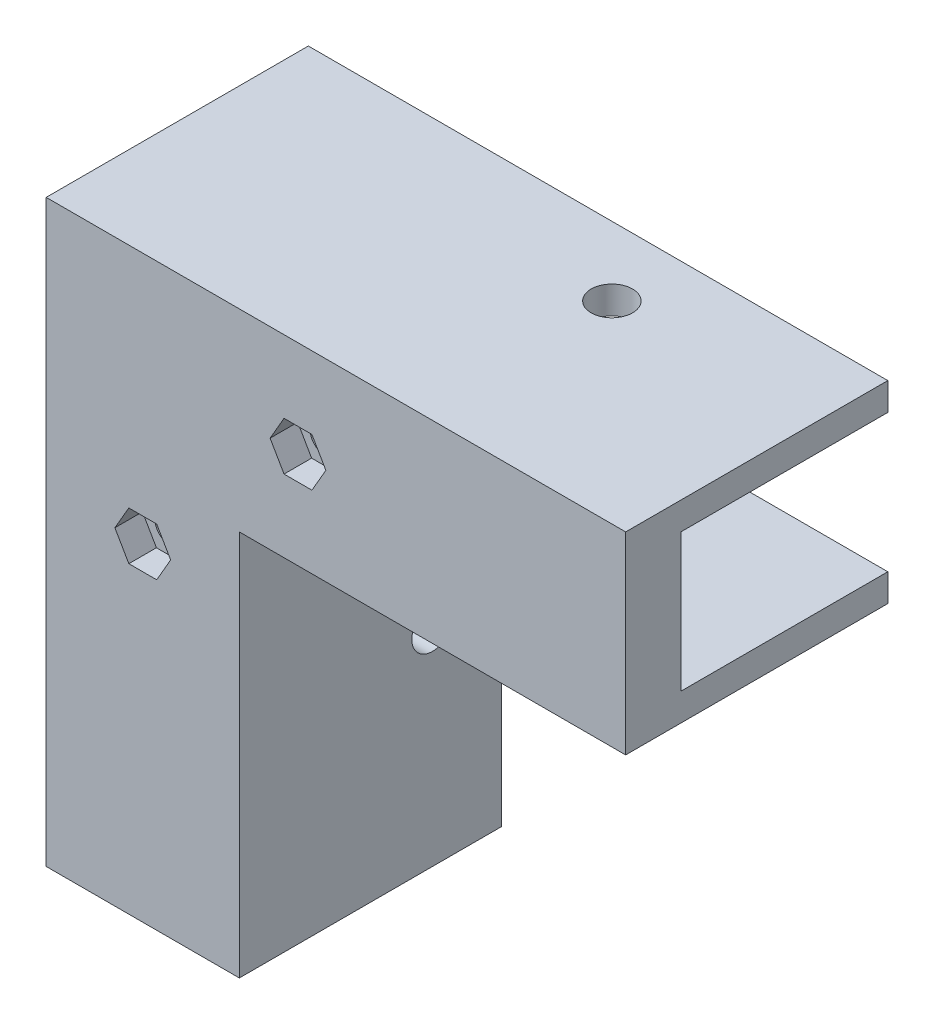
SolidWorks part; units mm, degrees
ref_plane "Plan de face" through (0, 0, 0) normal (0, 0, 1) x (1, 0, 0)
ref_plane "Plan de dessus" through (0, 0, 0) normal (0, 1, 0) x (1, 0, 0)
ref_plane "Plan de droite" through (0, 0, 0) normal (1, 0, 0) x (0, 0, -1)
sketch "Esquisse1" plane through (0, 0, 0) normal (0, 0, 1) x (1, 0, 0)
  line L0 (0, 0) -> (0, 60)
  line L1 (0, 60) -> (60, 60)
  line L2 (60, 60) -> (60, 80)
  line L3 (60, 80) -> (-20, 80)
  line L4 (-20, 80) -> (-20, 0)
  line L5 (-20, 0) -> (0, 0)
  dimension "D1" = 60
  dimension "D2" = 60
  dimension "D3" = 20
  dimension "D4" = 20
extrude "Boss.-Extru.1" add sketch "Esquisse1" along normal blind 8
sketch "Esquisse2" plane through (0, 0, 8) normal (0, 0, 1) x (1, 0, 0)
  line L0 (-12.0207, 51) -> (-7.9793, 44) construction
  line L1 (-20, 80) -> (-20, 0) construction
  line L3 (-5.9585, 47.5) -> (-14.0415, 47.5) construction
  line L5 (60, 80) -> (-20, 80) construction
  line L6 (0, 0) -> (0, 60) construction
  line L7 (-14.0415, 47.5) -> (-12.0207, 51)
  line L8 (-12.0207, 51) -> (-7.9793, 51)
  line L9 (-7.9793, 51) -> (-5.9585, 47.5)
  line L10 (-5.9585, 47.5) -> (-7.9793, 44)
  line L11 (-7.9793, 44) -> (-12.0207, 44)
  line L12 (-12.0207, 44) -> (-14.0415, 47.5)
  line L13 (10.4793, 66.5) -> (14.5207, 73.5) construction
  line L14 (16.5415, 70) -> (8.4585, 70) construction
  line L15 (-5.9585, 47.5) -> (-6.29, 47.0056)
  line L20 (-12.0207, 44) -> (-12.0207, 51) construction
  line L23 (8.4585, 70) -> (10.4793, 73.5)
  line L24 (10.4793, 73.5) -> (14.5207, 73.5)
  line L25 (14.5207, 73.5) -> (16.5415, 70)
  line L26 (16.5415, 70) -> (14.5207, 66.5)
  line L27 (14.5207, 66.5) -> (10.4793, 66.5)
  line L28 (10.4793, 66.5) -> (8.4585, 70)
  line L31 (16.5415, 70) -> (16.21, 69.5056)
  line L36 (10.4793, 66.5) -> (10.4793, 73.5) construction
  point P26 (-10, 47.5)
  point P27 (12.5, 70)
  dimension "D2" = 32.5
  dimension "D3" = 7
  dimension "D4" = 7
  dimension "D6" = 120
  dimension "D7" = 30
  dimension "D8" = 7
  dimension "D9" = 7
  dimension "D10" = 7
  dimension "D11" = 120
  dimension "D12" = 30
  dimension "D13" = 10
  dimension "D14" = 10
  dimension "D15" = 32.5
extrude "Enlèv. mat.-Extru.1" cut sketch "Esquisse2" against normal blind 4
sketch "Esquisse3" plane through (0, 0, 4) normal (0, 0, 1) x (1, 0, 0)
  line L0 (-7.9793, 51) -> (-5.9585, 47.5) construction
  line L1 (-14.0415, 47.5) -> (-12.0207, 51) construction
  line L3 (10.4793, 73.5) -> (14.5207, 73.5) construction
  line L4 (16.5415, 70) -> (14.5207, 66.5) construction
  circle A0 centre (-10, 47.5) radius 2.25
  circle A1 centre (12.5, 70) radius 2.25
  dimension "D1" = 3.5
  dimension "D2" = 3.5
  dimension "D3" = 4.5
  dimension "D4" = 4.5
  dimension "D5" = 3.5
  dimension "D6" = 3.5
extrude "Enlèv. mat.-Extru.2" cut sketch "Esquisse3" against normal through all
sketch "Esquisse4" plane through (0, 0, 8) normal (0, 0, 1) x (1, 0, 0)
  line L0 (0, 0) -> (0, 60)
  line L2 (0, 60) -> (60, 60)
  line L3 (60, 60) -> (60, 56)
  line L4 (60, 56) -> (4, 56)
  line L5 (4, 56) -> (4, 0)
  line L6 (4, 0) -> (0, 0)
  line L7 (60, 80) -> (60, 84)
  line L8 (60, 84) -> (-24, 84)
  line L9 (-24, 84) -> (-24, 0)
  line L10 (-24, 0) -> (-20, 0)
  line L11 (-20, 0) -> (-20, 80)
  line L12 (-20, 80) -> (60, 80)
  dimension "D1" = 4
  dimension "D2" = 4
  dimension "D3" = 4
  dimension "D4" = 4
extrude "Boss.-Extru.2" add sketch "Esquisse4" against normal blind 38
sketch "Esquisse5" plane through (0, 56, 0) normal (0, -1, 0) x (1, 0, 0)
  line L0 (4, -30) -> (60, -30) construction
  line L1 (60, -30) -> (60, 8) construction
  circle A0 centre (30, -20) radius 3
  dimension "D1" = 6
  dimension "D2" = 10
  dimension "D3" = 30
extrude "Enlèv. mat.-Extru.3" cut sketch "Esquisse5" against normal through all
sketch "Esquisse6" plane through (4, 0, 0) normal (1, 0, 0) x (0, 0, -1)
  line L0 (30, 0) -> (30, 56) construction
  line L1 (30, 0) -> (-8, 0) construction
  circle A0 centre (20, 30) radius 3
  dimension "D1" = 6
  dimension "D2" = 10
  dimension "D3" = 30
extrude "Enlèv. mat.-Extru.4" cut sketch "Esquisse6" against normal through all
